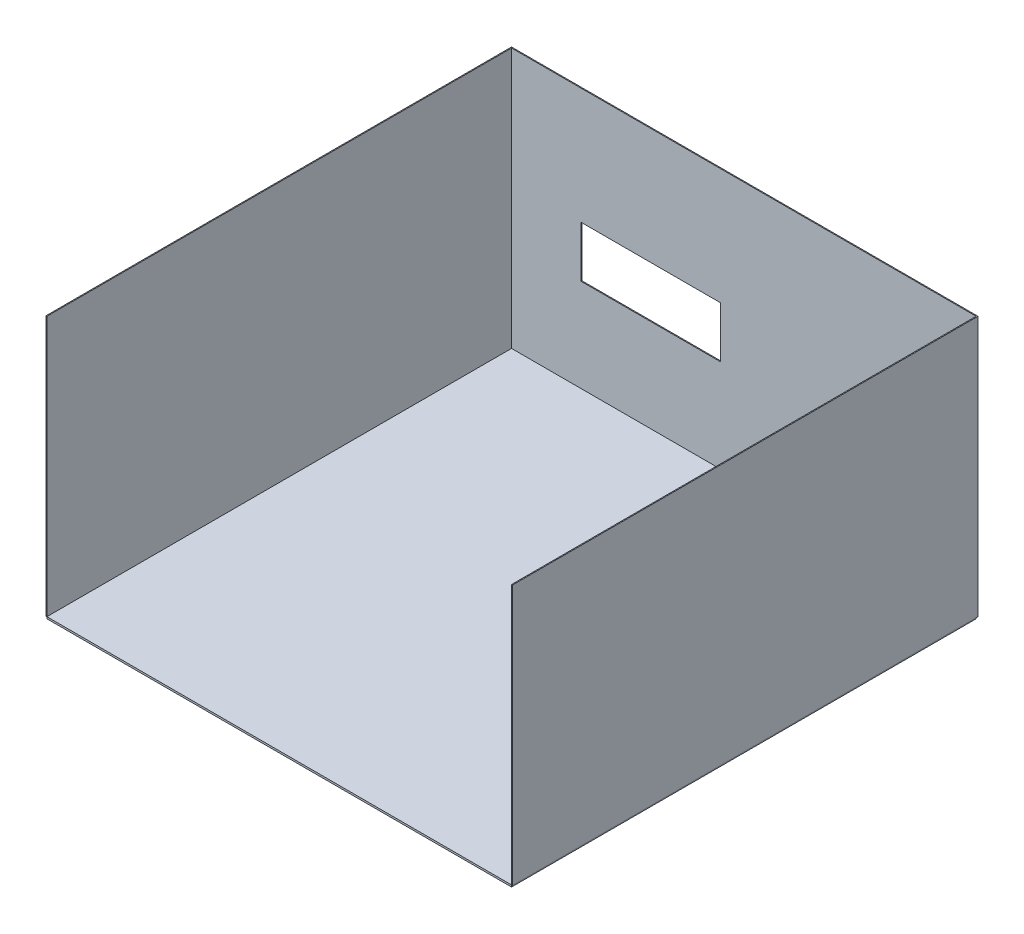
SolidWorks part; units mm, degrees
material "Mahogany"
ref_plane "Front Plane" through (0, 0, 0) normal (0, 0, 1) x (1, 0, 0)
ref_plane "Top Plane" through (0, 0, 0) normal (0, 1, 0) x (1, 0, 0)
ref_plane "Right Plane" through (0, 0, 0) normal (1, 0, 0) x (0, 0, -1)
sketch "Sketch1" plane through (0, 0, 0) normal (0, 1, 0) x (1, 0, 0)
  line L1 (-33700.6161, 2909.6455) -> (-28700.6161, 2909.6455)
  line L2 (-33700.6161, 2909.6455) -> (-33700.6161, -2090.3545)
  line L3 (-33700.6161, -2090.3545) -> (-28700.6161, -2090.3545)
  line L4 (-28700.6161, 2909.6455) -> (-28700.6161, -2090.3545)
  dimension "D1" = 5000
  dimension "D2" = 5000
extrude "Boss-Extrude1" add sketch "Sketch1" along normal blind 20 contours L2 L1 L4 L3
sketch "Sketch4" plane through (0, 20, 0) normal (0, 1, 0) x (1, 0, 0)
  line L6 (-33700.6161, 2909.6455) -> (-33700.6161, -2090.3545)
  line L7 (-33700.6161, 2909.6455) -> (-33700.6161, -2090.3545)
  line L9 (-28700.6161, 2909.6455) -> (-28700.6161, -2090.3545)
  line L10 (-28700.6161, 2909.6455) -> (-28700.6161, -2090.3545)
  line L12 (-33700.6161, 2909.6455) -> (-28700.6161, 2909.6455)
  line L13 (-33700.6161, 2909.6455) -> (-28700.6161, 2909.6455)
  dimension "D1" = 0
  dimension "D2" = 0
  dimension "D3" = 0
extrude "Extrude-Thin1" add sketch "Sketch4" along normal blind 2800 thin
sketch "Sketch5" plane through (0, 0, -2909.6455) normal (0, 0, 1) x (1, 0, 0)
  line L0 (-33700.6161, 2820) -> (-33700.6161, 20) construction
  line L1 (-32950.6161, 1570) -> (-31450.6161, 1570)
  line L2 (-32950.6161, 1570) -> (-32950.6161, 1020)
  line L3 (-32950.6161, 1020) -> (-31450.6161, 1020)
  line L4 (-31450.6161, 1570) -> (-31450.6161, 1020)
  line L5 (-33700.6161, 20) -> (-28700.6161, 20) construction
  dimension "D1" = 1500
  dimension "D2" = 550
  dimension "D3" = 750
  dimension "D4" = 1000
extrude "Cut-Extrude1" cut sketch "Sketch5" against normal blind 10
equation "\"WallHeight\"= 280"
equation "\"D1@Extrude-Thin1\"=\"WallHeight\""
